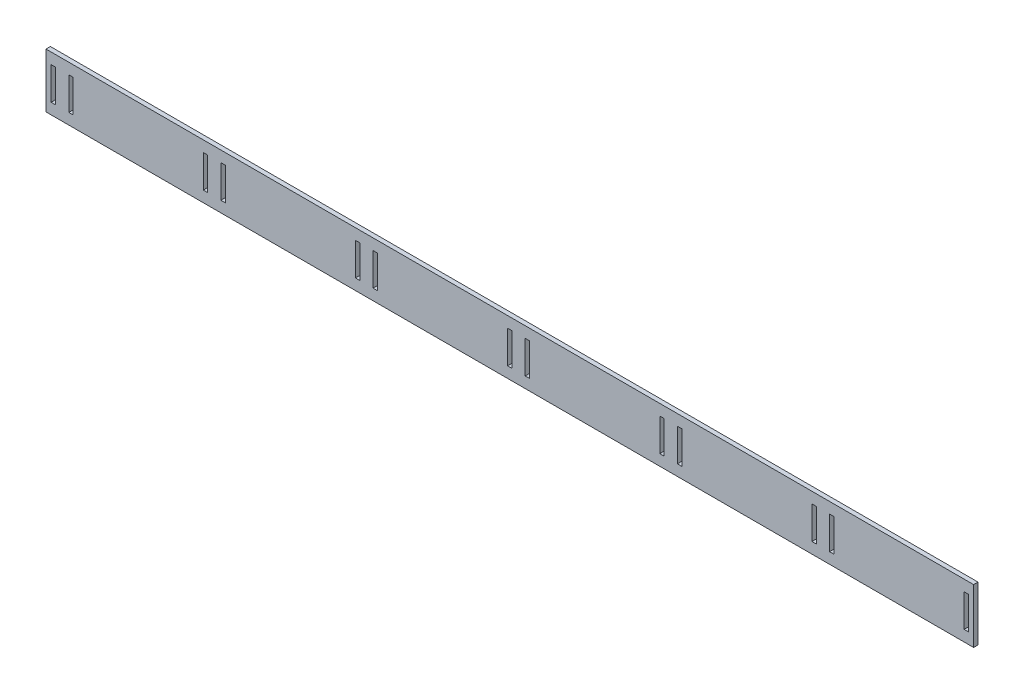
SolidWorks part; units mm, degrees
ref_plane "Front Plane" through (0, 0, 0) normal (0, 0, 1) x (1, 0, 0)
ref_plane "Top Plane" through (0, 0, 0) normal (0, 1, 0) x (1, 0, 0)
ref_plane "Right Plane" through (0, 0, 0) normal (1, 0, 0) x (0, 0, -1)
sketch "Sketch2" plane through (0, 0, 0) normal (0, 0, 1) x (1, 0, 0)
  line L0 (0, -24.9) -> (424, -24.9)
  line L1 (0, 0) -> (424, 0)
  line L2 (0, 0) -> (0, -24.9)
  line L3 (2.35, -19.9) -> (4.35, -19.9)
  line L4 (424, 0) -> (424, -24.9)
  line L5 (2.35, -5) -> (2.35, -19.9)
  line L6 (0, 0) -> (0, -24.9)
  line L8 (4.35, -5) -> (4.35, -19.9)
  line L9 (71.9, -5) -> (71.9, -19.9)
  line L10 (12.4, -5) -> (12.4, -19.9)
  line L11 (10.4, -5) -> (12.4, -5)
  line L12 (358.15, -5) -> (360.15, -5)
  line L13 (79.95, -5) -> (81.95, -5)
  line L14 (73.9, -5) -> (73.9, -19.9)
  line L15 (10.4, -5) -> (10.4, -19.9)
  line L16 (350.1, -5) -> (352.1, -5)
  line L17 (288.6, -5) -> (290.6, -5)
  line L18 (79.95, -5) -> (79.95, -19.9)
  line L19 (81.95, -5) -> (81.95, -19.9)
  line L22 (141.45, -5) -> (141.45, -19.9)
  line L23 (2.35, -5) -> (4.35, -5)
  line L24 (143.45, -5) -> (143.45, -19.9)
  line L27 (149.5, -5) -> (149.5, -19.9)
  line L28 (151.5, -5) -> (151.5, -19.9)
  line L31 (211, -5) -> (211, -19.9)
  line L32 (213, -5) -> (213, -19.9)
  line L35 (219.05, -5) -> (219.05, -19.9)
  line L36 (221.05, -5) -> (221.05, -19.9)
  line L39 (280.55, -5) -> (280.55, -19.9)
  line L40 (282.55, -5) -> (282.55, -19.9)
  line L41 (288.6, -5) -> (288.6, -19.9)
  line L42 (290.6, -5) -> (290.6, -19.9)
  line L45 (350.1, -5) -> (350.1, -19.9)
  line L46 (352.1, -5) -> (352.1, -19.9)
  line L49 (358.15, -5) -> (358.15, -19.9)
  line L50 (360.15, -5) -> (360.15, -19.9)
  line L53 (419.65, -5) -> (419.65, -19.9)
  line L54 (421.65, -5) -> (421.65, -19.9)
  line L60 (2.35, -5) -> (4.35, -5)
  line L61 (71.9, -5) -> (73.9, -5)
  line L62 (280.55, -5) -> (282.55, -5)
  line L63 (219.05, -5) -> (221.05, -5)
  line L64 (211, -5) -> (213, -5)
  line L65 (149.5, -5) -> (151.5, -5)
  line L66 (141.45, -5) -> (143.45, -5)
  line L71 (419.65, -5) -> (421.65, -5)
  line L84 (0, -5) -> (424, -5) construction
  line L85 (10.4, -19.9) -> (12.4, -19.9)
  line L86 (0, -19.9) -> (424, -19.9) construction
  line L87 (71.9, -19.9) -> (73.9, -19.9)
  line L88 (10.4, -5) -> (12.4, -5)
  line L89 (71.9, -5) -> (73.9, -5)
  line L90 (79.95, -19.9) -> (81.95, -19.9)
  line L95 (141.45, -19.9) -> (143.45, -19.9)
  line L96 (141.45, -5) -> (143.45, -5)
  line L97 (79.95, -5) -> (81.95, -5)
  line L98 (149.5, -19.9) -> (151.5, -19.9)
  line L99 (149.5, -5) -> (151.5, -5)
  line L100 (211, -5) -> (213, -5)
  line L101 (211, -19.9) -> (213, -19.9)
  line L102 (280.55, -5) -> (290.6, -5)
  line L103 (280.55, -19.9) -> (282.55, -19.9)
  line L104 (219.05, -19.9) -> (221.05, -19.9)
  line L105 (219.05, -5) -> (221.05, -5)
  line L106 (350.1, -5) -> (352.1, -5)
  line L107 (350.1, -19.9) -> (352.1, -19.9)
  line L108 (288.6, -19.9) -> (290.6, -19.9)
  line L109 (419.65, -19.9) -> (421.65, -19.9)
  line L110 (358.15, -19.9) -> (360.15, -19.9)
  line L111 (358.15, -5) -> (360.15, -5)
  line L112 (419.65, -5) -> (421.65, -5)
  point P22 (0, -58)
  point P23 (424, -58)
  point P24 (0, -56)
  point P27 (424, -56)
  point P59 (-144.1331, -129.2938)
  point P60 (247.4863, -129.2938)
  point P63 (2.35, -9.75)
  point P64 (247.4863, -109.0438)
extrude "Boss-Extrude1" add sketch "Sketch2" along normal blind 2
